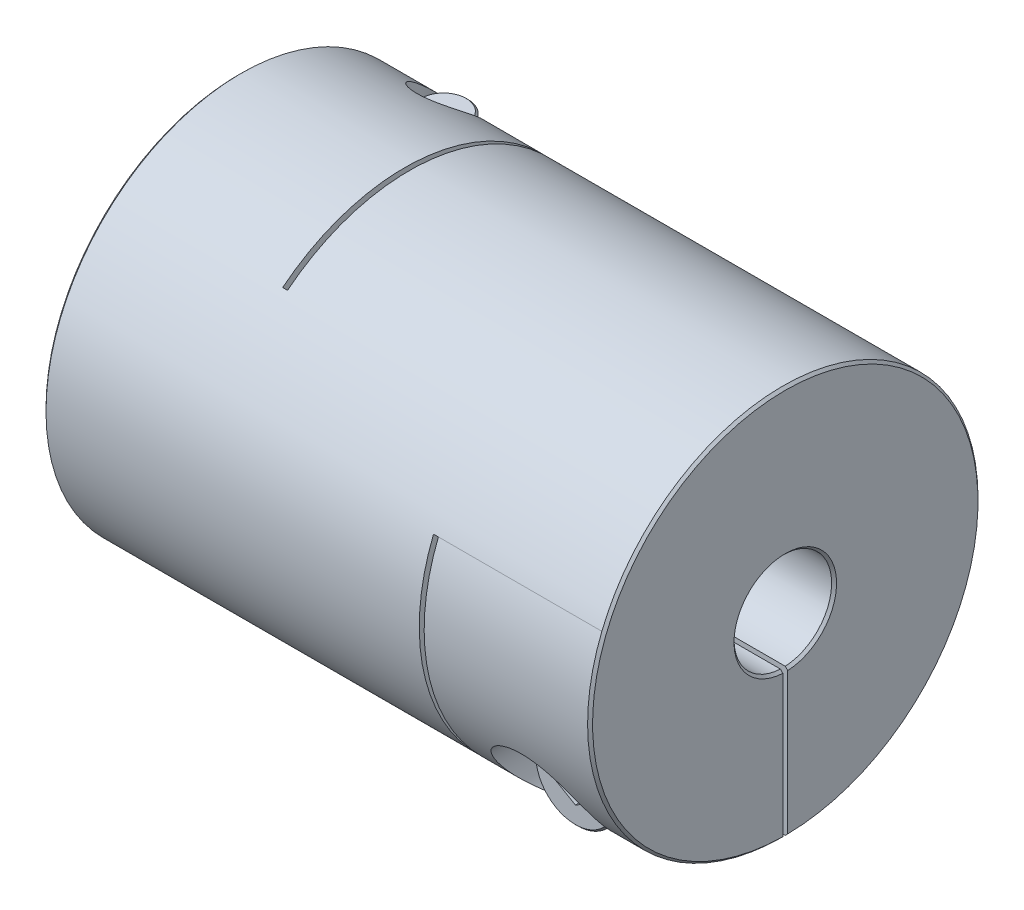
SolidWorks part; units mm, degrees
ref_plane "Front Plane" through (0, 0, 0) normal (0, 0, 1) x (1, 0, 0)
ref_plane "Top Plane" through (0, 0, 0) normal (0, 1, 0) x (1, 0, 0)
ref_plane "Right Plane" through (0, 0, 0) normal (1, 0, 0) x (0, 0, -1)
sketch "Sketch1" plane through (0, 0, 0) normal (1, 0, 0) x (0, 0, -1)
  circle A0 centre (0, 0) radius 20
  dimension "dim D" = 40
extrude "Boss-Extrude1" add sketch "Sketch1" along normal mid plane 56
sketch "Sketch2" plane through (28, 0, 0) normal (1, 0, 0) x (0, 0, -1)
  circle A0 centre (0, 0) radius 5
  dimension "dim D1" = 10
extrude "Cut-Extrude1" cut sketch "Sketch2" against normal through all
chamfer "Chamfer1" distance 0.254 angle 45 4 edges at (-28, 0, -5) (-28, 0, -20) (28, 0, -20) (28, 0, -5)
ref_plane "Plane2" through (0, -20, 0) normal (0, -1, 0) x (1, 0, 0)
ref_plane "L1" through (-19.5, 0, 0) normal (-1, 0, 0) x (0, 0, 1)
sketch "Sketch4" plane through (0, -20, 0) normal (0, -1, 0) x (1, 0, 0)
  line L0 (-27.746, -20) -> (27.746, -20) construction
  line L1 (-11, -20) -> (-10.5, -20)
  line L2 (-11, -20) -> (-11, 12.5)
  line L3 (-11, 12.5) -> (-10.5, 12.5)
  line L4 (-10.5, -20) -> (-10.5, 12.5)
  line L5 (-11, 5) -> (-11, 20) construction
  line L6 (27.746, 5) -> (-27.746, 5) construction
  line L7 (27.746, 20) -> (-27.746, 20) construction
  line L10 (-11, 12.5) -> (-28, 12.5) construction
  line L11 (-28, 19.746) -> (-28, -19.746) construction
  line L12 (-19.5, 10.2256) -> (-19.5, -10.2256) construction
  point P16 (-19.5, 12.5)
  dimension "D1" = 0.5
extrude "Cut-Extrude2" cut sketch "Sketch4" against normal through all
ref_plane "Plane4" through (0, 0, -20) normal (0, 0, -1) x (-1, 0, 0)
sketch "Sketch7" plane through (0, 0, -20) normal (0, 0, -1) x (-1, 0, 0)
  line L1 (-10.5, -20) -> (-11, -20)
  line L2 (-11, -20) -> (-11, 7.5)
  line L3 (-11, 7.5) -> (-10.5, 7.5)
  line L4 (-10.5, -20) -> (-10.5, 7.5)
  line L5 (28, 8.6487) -> (19.5, 8.6487) construction
  line L7 (-10.505, -20) -> (10.505, -20) construction
  line L8 (-27.746, -5) -> (10.5, -5) construction
  line L9 (28, -19.746) -> (28, 19.746) construction
  line L10 (-27.746, -5) -> (10.5, -5) construction
  line L11 (10.5, 15.6125) -> (11, 15.6125) construction
  line L12 (-11, 7.5) -> (-11, -20) construction
  line L14 (-27.746, -5) -> (10.5, -5) construction
  line L16 (-27.746, -5) -> (10.5, -5) construction
  line L17 (11, -20) -> (27.746, -20) construction
  line L18 (19.5, -10.2256) -> (19.5, 10.2256) construction
  line L19 (-27.746, -20) -> (-27.746, 20) construction
  line L20 (-28, 7.5) -> (-19.5, 7.5) construction
  line L21 (-28, 19.746) -> (-28, -19.746) construction
  line L22 (-19.5, 7.5) -> (-11, 7.5) construction
  line L23 (-27.746, -20) -> (-27.746, 20) construction
  line L24 (-27.746, -5) -> (-27.746, 20) construction
  line L25 (-27.746, -5) -> (10.5, -5) construction
  point P23 (-11, 7.5)
  point P33 (-27.746, 7.5)
extrude "Cut-Extrude3" cut sketch "Sketch7" against normal through all
sketch "Sketch8" plane through (0, 0, 0) normal (0, 1, 0) x (1, 0, 0)
  line L0 (-11, -12.5) -> (-11, 20) construction
  line L1 (-28, 20) -> (-11, 20)
  line L2 (-28, 20) -> (-28, 0)
  line L3 (-28, 0) -> (-11, 0)
  line L4 (-11, 20) -> (-11, 0)
  line L5 (10.505, 20) -> (-10.505, 20) construction
  line L6 (-28, 19.746) -> (-28, -19.746) construction
extrude "Cut-Extrude5" cut sketch "Sketch8" against normal mid plane 0.5
sketch "Sketch13" plane through (0, 0, 0) normal (0, 0, 1) x (1, 0, 0)
  line L0 (28, -19.746) -> (28, 19.746) construction
  line L1 (11, -20) -> (28, -20)
  line L2 (11, -20) -> (11, 0)
  line L3 (11, 0) -> (28, 0)
  line L4 (28, -20) -> (28, 0)
extrude "Cut-Extrude6" cut sketch "Sketch13" against normal mid plane 0.5
hole_wizard "CBORE for M5 SHCS1" positions "Sketch12" profile "Sketch11" counterbore size "M5" standard "Ansi Metric" end condition through all
sketch "Sketch12" plane through (0, -20, 0) normal (0, -1, 0) x (1, 0, 0)
  line L0 (-19.5, 10.2256) -> (-19.5, -10.2256) construction
  line L1 (-11, -4.9937) -> (-11, -19.9984) construction
  line L2 (-11, -4.9937) -> (-11, -19.9984)
  line L3 (-11, -12.4961) -> (-19.5, -12.4961) construction
  point P0 (-19.5, -12.4961)
sketch "Sketch11" plane through (-19.5, -20, -12.4961) normal (1, 0, 0) x (0, 0, -1)
  line L0 (0, 0) -> (0, 40)
  line L1 (0, 40) -> (2.75, 40)
  line L3 (2.75, 40) -> (2.75, 12)
  line L4 (2.75, 12) -> (5, 12)
  line L5 (5, 12) -> (5, 0)
  line L7 (5, 0) -> (0, 0)
  line L11 (0, -6.35) -> (0, 107.95) construction
  dimension "Thru Hole Dia." = 5.5
  dimension "Thru Hole Depth" = 40
  dimension "C'Bore Dia." = 10
  dimension "C'Bore Depth" = 12
ref_plane "Plane5" through (0, 0, 20) normal (0, 0, 1) x (1, 0, 0)
hole_wizard "CBORE for M5 SHCS2" positions "Sketch15" profile "Sketch14" counterbore size "M5" standard "Ansi Metric" end condition through all
sketch "Sketch15" plane through (0, 0, 20) normal (0, 0, 1) x (1, 0, 0)
  line L0 (-24.5, -8) -> (-14.5, -8) construction
  line L1 (-24.5, -8) -> (-14.5, -8)
  line L5 (0, 0) -> (0, 20) construction
  line L6 (-11, 20) -> (-27.746, 20) construction
  line L8 (24.5, -8) -> (14.5, -8)
  line L9 (19.5, -8) -> (19.5, -12.4961) construction
  line L11 (19.5, -19.9984) -> (19.5, -4.9937) construction
  line L12 (27.746, -19.9984) -> (11, -19.9984) construction
  line L13 (11, -4.9937) -> (27.746, -4.9937) construction
  point P0 (19.5, -12.4961)
sketch "Sketch14" plane through (19.5, -12.4961, 20) normal (1, 0, 0) x (0, -1, 0)
  line L0 (0, 0) -> (0, 40)
  line L1 (0, 40) -> (2.75, 40)
  line L3 (2.75, 40) -> (2.75, 12)
  line L4 (2.75, 12) -> (5, 12)
  line L5 (5, 12) -> (5, 0)
  line L7 (5, 0) -> (0, 0)
  line L11 (0, -6.35) -> (0, 107.95) construction
  dimension "Thru Hole Dia." = 5.5
  dimension "Thru Hole Depth" = 40
  dimension "C'Bore Dia." = 10
  dimension "C'Bore Depth" = 12
sketch "Sketch16" plane through (0, 0, 8) normal (0, 0, 1) x (1, 0, 0)
  circle A0 centre (19.5, -12.4961) radius 4.25
  dimension "screw dia" = 8.5
extrude "Boss-Extrude2" add sketch "Sketch16" along normal blind 5 separate body
sketch "Sketch17" plane through (0, 0, 8) normal (0, 0, -1) x (-1, 0, 0)
  circle A0 centre (-19.5, -12.4961) radius 2.5
  dimension "D1" = 5
extrude "Boss-Extrude3" add sketch "Sketch17" along normal blind 22.5
chamfer "Chamfer2" distance 0.2 angle 45 3 edges at (17, -12.4961, -14.5) (23.75, -12.4961, 8) (23.75, -12.4961, 13)
sketch "Sketch18" plane through (0, 0, 13) normal (0, 0, 1) x (1, 0, 0)
  line L1 (19.5, -14.8055) -> (21.5, -13.6508)
  line L2 (21.5, -13.6508) -> (21.5, -11.3414)
  line L3 (21.5, -11.3414) -> (19.5, -10.1867)
  line L4 (19.5, -10.1867) -> (17.5, -11.3414)
  line L5 (17.5, -11.3414) -> (17.5, -13.6508)
  line L6 (17.5, -13.6508) -> (19.5, -14.8055)
  circle A0 centre (19.5, -12.4961) radius 2 construction
  dimension "hex" = 4
extrude "Cut-Extrude7" cut sketch "Sketch18" against normal blind 1.5
mirror "Mirror1" about plane through (0, 0, 0) normal (1, 0, 0) of bodies 121
pattern_circular "CirPattern1" count 2 every 90 about axis through (0, 0, 0) along (1, 0, 0) of bodies 122
delete or keep bodies "Body-Delete1" type delete bodies bodies 122
